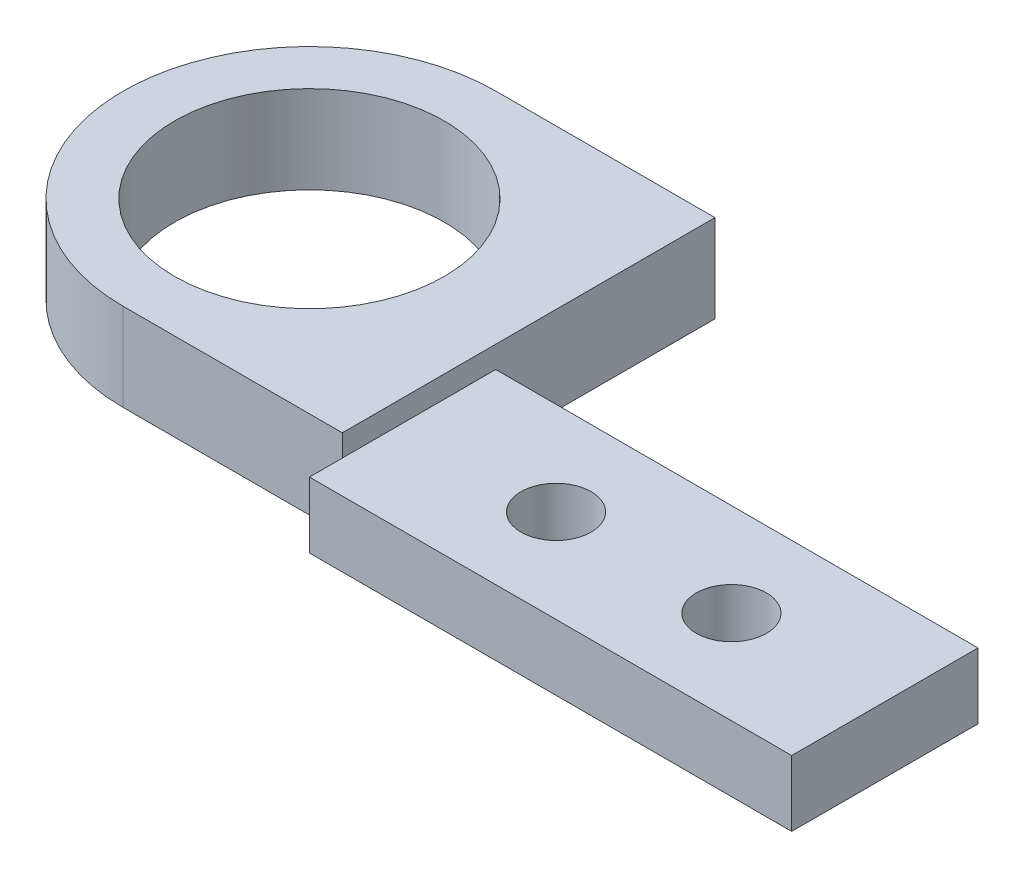
SolidWorks part; units mm, degrees
ref_plane "Front Plane" through (0, 0, 0) normal (0, 0, 1) x (1, 0, 0)
ref_plane "Top Plane" through (0, 0, 0) normal (0, 1, 0) x (1, 0, 0)
ref_plane "Right Plane" through (0, 0, 0) normal (1, 0, 0) x (0, 0, -1)
sketch "Sketch1" plane through (0, 0, 0) normal (0, 1, 0) x (1, 0, 0)
  line L0 (10, -1.5) -> (32, -1.5)
  line L1 (0, -8.5) -> (10, -8.5)
  line L4 (32, -8.5) -> (32, -1.5)
  line L6 (0, -8.5) -> (10, -8.5)
  line L7 (0, -8.5) -> (0, -6.15)
  line L8 (0, 8.5) -> (10, 8.5)
  line L9 (10, -1.5) -> (10, 8.5)
  line L11 (10, -8.5) -> (10, -10)
  line L12 (10, -10) -> (32, -10)
  line L13 (32, -8.5) -> (32, -10)
  arc A0 (0, 8.5) -> (0, -8.5) centre (0, 0) ccw
  circle A1 centre (0, 0) radius 6.15
  dimension "D1" = 17
  dimension "D3" = 12.3
  dimension "D2" = 22
  dimension "D4" = 10
  dimension "D5" = 17
  dimension "D6" = 7
  dimension "D7" = 1.5
extrude "Boss-Extrude2" add sketch "Sketch1" along normal blind 4
sketch "Sketch4" plane through (0, 4, 0) normal (0, 1, 0) x (1, 0, 0)
  line L1 (10, -10) -> (32, -10)
  line L2 (10, -10) -> (10, -1.5)
  line L3 (10, -1.5) -> (32, -1.5)
  line L4 (32, -10) -> (32, -1.5)
extrude "Cut-Extrude2" cut sketch "Sketch4" against normal blind 1
sketch "Sketch5" plane through (0, 0, 0) normal (0, -1, 0) x (1, 0, 0)
  line L0 (10, 8.5) -> (10, 10) construction
  line L1 (10, 10) -> (32, 10) construction
  line L2 (10, 1.5) -> (32, 1.5) construction
  line L3 (32, 1.5) -> (32, 10) construction
  circle A0 centre (17, 5.75) radius 1.6
  circle A1 centre (25, 5.75) radius 1.6
  dimension "D1" = 3.2
  dimension "D6" = 3.2
  dimension "D2" = 7
  dimension "D3" = 4.25
  dimension "D4" = 4.25
  dimension "D5" = 7
extrude "Cut-Extrude3" cut sketch "Sketch5" against normal through all
